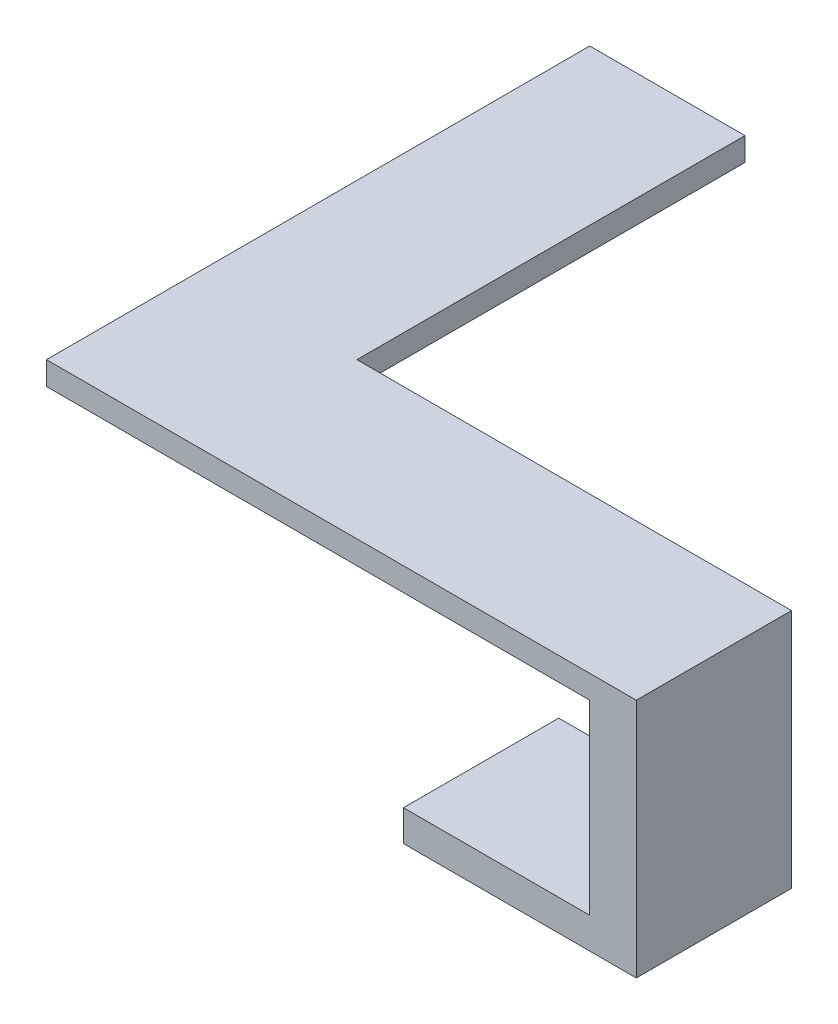
SolidWorks part; units mm, degrees
ref_plane "Front Plane" through (0, 0, 0) normal (0, 0, 1) x (1, 0, 0)
ref_plane "Top Plane" through (0, 0, 0) normal (0, 1, 0) x (1, 0, 0)
ref_plane "Right Plane" through (0, 0, 0) normal (1, 0, 0) x (0, 0, -1)
sketch "Sketch1" plane through (0, 0, 0) normal (0, 1, 0) x (1, 0, 0)
  line L0 (-10.529, 3.7604) -> (-10.529, 28.7604)
  line L1 (-20.529, -6.2396) -> (17.471, -6.2396)
  line L3 (-10.529, 3.7604) -> (17.471, 3.7604)
  line L4 (17.471, -6.2396) -> (17.471, 3.7604)
  line L5 (-4.3891, -0.9447) -> (17.471, 3.7604) construction
  line L6 (-10.529, 3.7604) -> (17.471, -6.2396) construction
  line L7 (-10.529, 28.7604) -> (-20.529, 28.7604)
  line L8 (-20.529, 28.7604) -> (-20.529, -6.2396)
  point P0 (0, 0)
  dimension "D1" = 10
  dimension "D2" = 28
  dimension "D3" = 270
  dimension "D4" = 25
  dimension "D5" = 10
extrude "Boss-Extrude1" add sketch "Sketch1" along normal blind 1.5
sketch "Sketch2" plane through (0, 0, 0) normal (0, -1, 0) x (1, 0, 0)
  line L0 (17.471, -3.7604) -> (-10.529, -3.7604) construction
  line L1 (17.471, 6.2396) -> (14.471, 6.2396)
  line L2 (17.471, 6.2396) -> (17.471, -3.7604)
  line L3 (17.471, -3.7604) -> (14.471, -3.7604)
  line L4 (14.471, 6.2396) -> (14.471, -3.7604)
  dimension "D1" = 3
extrude "Boss-Extrude2" add sketch "Sketch2" along normal blind 14
sketch "Sketch3" plane through (14.471, 0, 0) normal (-1, 0, 0) x (0, 0, 1)
  line L0 (6.2396, -14) -> (6.2396, 0) construction
  line L1 (-3.7604, -14) -> (6.2396, -14)
  line L2 (-3.7604, -14) -> (-3.7604, -12)
  line L3 (-3.7604, -12) -> (6.2396, -12)
  line L4 (6.2396, -14) -> (6.2396, -12)
  dimension "D1" = 2
extrude "Boss-Extrude3" add sketch "Sketch3" along normal blind 12
